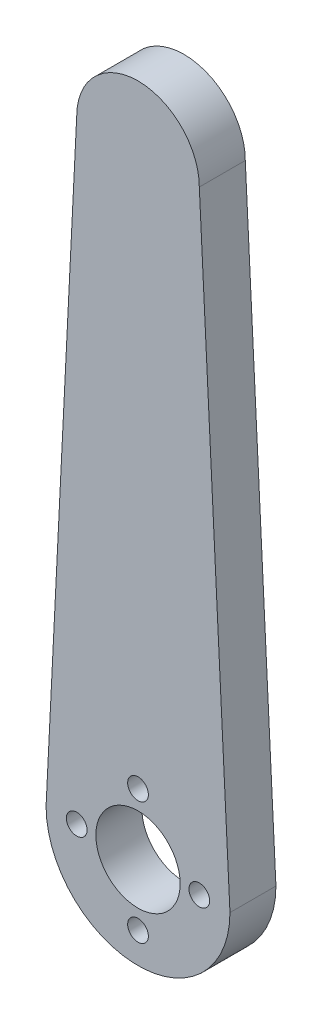
SolidWorks part; units mm, degrees
ref_plane "Front" through (0, 0, 0) normal (0, 0, 1) x (1, 0, 0)
ref_plane "Top" through (0, 0, 0) normal (0, 1, 0) x (1, 0, 0)
ref_plane "Right" through (0, 0, 0) normal (1, 0, 0) x (0, 0, -1)
sketch "Esquisse1" plane through (0, 0, 0) normal (0, 0, 1) x (1, 0, 0)
  line L0 (0, 0) -> (0, 80) construction
  line L1 (12, 0) -> (8, 80)
  line L2 (0, 58) -> (0, 80) construction
  line L3 (0, -12) -> (0, 0) construction
  line L4 (12, 0) -> (-12, 0) construction
  line L5 (8, 80) -> (-8, 80) construction
  line L6 (-12, 0) -> (-8, 80)
  arc A0 (8, 80) -> (-8, 80) centre (0, 80) ccw
  arc A1 (12, 0) -> (-12, 0) centre (0, 0) cw
  dimension "D2" = 12
  dimension "D3" = 8
  dimension "D1" = 80
extrude "Boss.-Extru.1" add sketch "Esquisse1" along normal blind 6
sketch "Esquisse2" plane through (0, 0, 6) normal (0, 0, 1) x (1, 0, 0)
  line L0 (0, 0) -> (8, 0) construction
  circle A0 centre (0, 0) radius 5.5
  circle A1 centre (8, 0) radius 1.35
  circle A2 centre (0, -8) radius 1.35
  circle A3 centre (-8, 0) radius 1.35
  circle A4 centre (0, 8) radius 1.35
  point P14 (0, 0)
  dimension "D1" = 11
  dimension "D2" = 2.7
  dimension "D3" = 8
  dimension "D4" = 4
extrude "Enlèv. mat.-Extru.1" cut sketch "Esquisse2" against normal through all both and the other way through all
